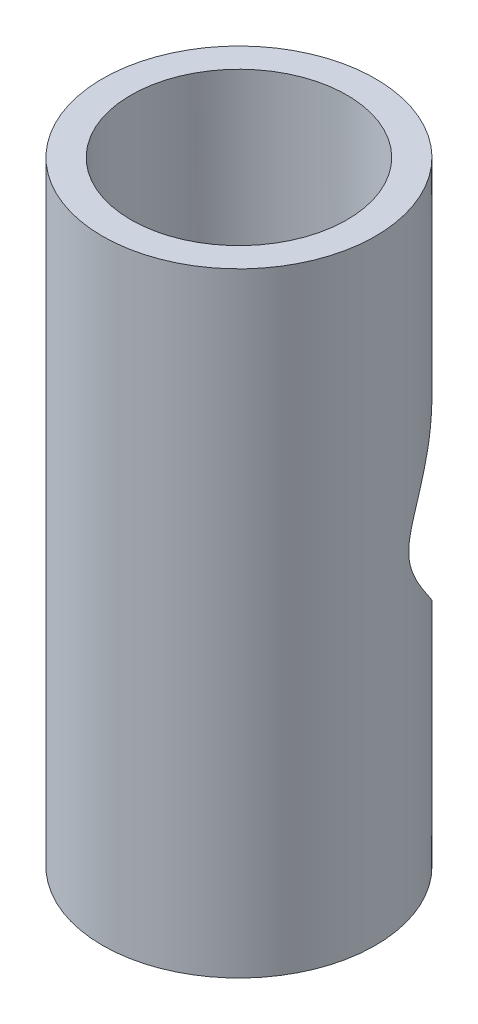
SolidWorks part; units mm, degrees
ref_plane "Front Plane" through (0, 0, 0) normal (0, 0, 1) x (1, 0, 0)
ref_plane "Top Plane" through (0, 0, 0) normal (0, 1, 0) x (1, 0, 0)
ref_plane "Right Plane" through (0, 0, 0) normal (1, 0, 0) x (0, 0, -1)
sketch "Sketch1" plane through (0, 0, 0) normal (0, 1, 0) x (1, 0, 0)
  circle A0 centre (0, 0) radius 15.24
  dimension "D1" = 30.48
extrude "Boss-Extrude1" add sketch "Sketch1" along normal blind 68.58
sketch "Sketch2" plane through (0, 0, 0) normal (0, 0, 1) x (1, 0, 0)
  line L4 (15.24, 68.58) -> (-15.24, 68.58) construction
  line L5 (-15.24, 0) -> (15.24, 0) construction
  circle A0 centre (0, 35.56) radius 14.605
  dimension "D1" = 29.21
  dimension "D2" = 35.56
extrude "Cut-Extrude1" cut sketch "Sketch2" against normal blind 68.58
sketch "Sketch3" plane through (0, 68.58, 0) normal (0, 1, 0) x (-1, 0, 0)
  circle A0 centre (0, 0) radius 12.065
  dimension "D1" = 24.13
extrude "Cut-Extrude2" cut sketch "Sketch3" against normal blind 68.58
